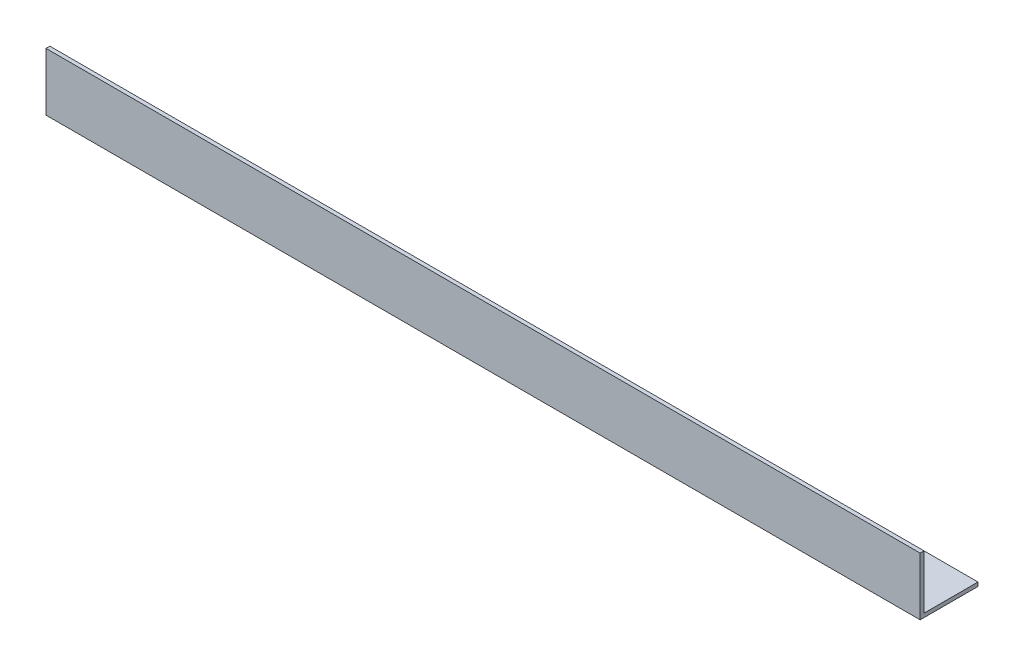
SolidWorks part; units mm, degrees
ref_plane "Спереди" through (0, 0, 0) normal (0, 0, 1) x (1, 0, 0)
ref_plane "Сверху" through (0, 0, 0) normal (0, 1, 0) x (1, 0, 0)
ref_plane "Справа" through (0, 0, 0) normal (1, 0, 0) x (0, 0, -1)
sketch "Эскиз1" plane through (0, 0, 0) normal (1, 0, 0) x (0, 0, -1)
  line L0 (0, 0) -> (0, 45)
  line L1 (0, 0) -> (45, 0)
extrude "Вытянуть-Тонкостенный1" add sketch "Эскиз1" along normal blind 680 thin
